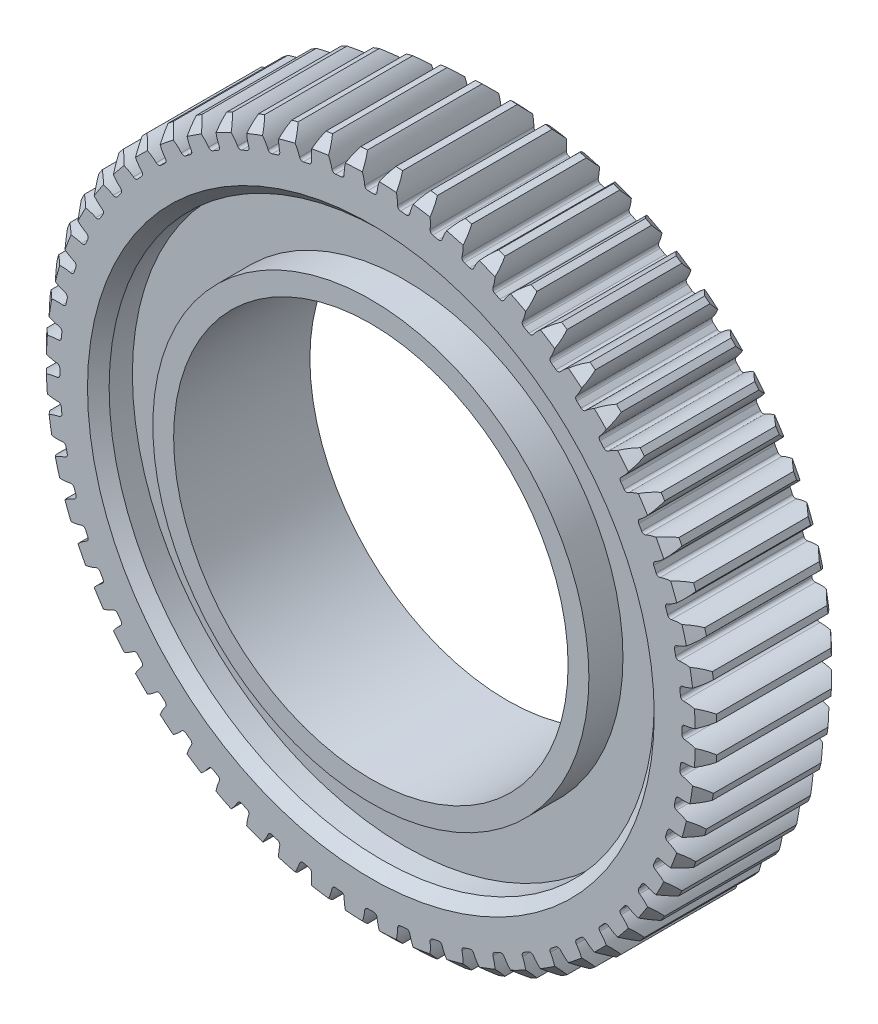
SolidWorks part; units mm, degrees
ref_plane "Front Plane" through (0, 0, 0) normal (0, 0, 1) x (1, 0, 0)
ref_plane "Top Plane" through (0, 0, 0) normal (0, 1, 0) x (1, 0, 0)
ref_plane "Right Plane" through (0, 0, 0) normal (1, 0, 0) x (0, 0, -1)
sketch "Sketch1" plane through (0, 0, 0) normal (0, 0, 1) x (1, 0, 0)
  circle A0 centre (0, 0) radius 47.625 construction
  circle A1 centre (0, 0) radius 49.2125
  dimension "D1" = 95.25
  dimension "D2" = 98.425
extrude "Boss-Extrude1" add sketch "Sketch1" along normal mid plane 20
sketch "Sketch2" plane through (0, 0, 0) normal (0, 0, 1) x (1, 0, 0)
  line L0 (0, 49.2125) -> (0, 0) construction
  line L1 (0, 0) -> (5.1441, 48.9429) construction
  line L2 (0, 0) -> (2.5756, 49.1451) construction
  line L3 (0, 0) -> (-0.8785, 45.6322) construction
  line L4 (-1.2467, 47.6087) -> (1.2467, 47.6087) construction
  line L5 (1.2467, 47.6087) -> (3.7366, 47.4782) construction
  line L6 (-1.8182, 49.1789) -> (0, 44.1835) construction
  circle A0 centre (0, 0) radius 46.0375 construction
  arc A2 (0.8785, 45.6322) -> (-0.8785, 45.6322) centre (0, 0) ccw
  circle A3 centre (0, 0) radius 49.2125 construction
  arc A4 (-0.8785, 45.6322) -> (-2.087, 49.1682) centre (-7.0009, 45.5143) ccw
  arc A5 (0.8785, 45.6322) -> (2.087, 49.1682) centre (7.0009, 45.5143) cw
  circle A6 centre (0, 0) radius 47.625 construction
  circle A7 centre (0, 0) radius 49.2125 construction
  arc A8 (5.1441, 48.9429) -> (-2.087, 49.1682) centre (0, 0) ccw
  dimension "D1" = 6
  dimension "D2" = 3.175
  dimension "D3" = 3.5719
  dimension "D4" = 20
extrude "Cut-Extrude1" cut sketch "Sketch2" against normal through all both and the other way through all contours A5 A8 A4 A2
chamfer "Chamfer1" distance 1.5875 2 edges at (0, -49.2125, 10) (0, -49.2125, -10)
fillet "Fillet1" radius 0.4762 2 edges at (0.8785, 45.6322, 0) (-0.8785, 45.6322, 0)
pattern_circular "CirPattern1" count 60 over 360 about axis through (0, 0, 0) along (0, 0, 1) of "Fillet1", "Cut-Extrude1"
sketch "Sketch3" plane through (0, 0, 10) normal (0, 0, 1) x (1, 0, 0)
  circle A0 centre (0, 0) radius 27
  dimension "D1" = 54
extrude "Cut-Extrude2" cut sketch "Sketch3" against normal blind 54
sketch "Sketch4" plane through (0, 0, 10) normal (0, 0, 1) x (1, 0, 0)
  circle A0 centre (0, 0) radius 27
  circle A1 centre (0, 0) radius 32
  circle A2 centre (0, 0) radius 40
  dimension "D1" = 80
  dimension "D2" = 54
  dimension "D3" = 5
extrude "Cut-Extrude3" cut sketch "Sketch4" against normal blind 5 contours A2 A1
mirror "Mirror1" about plane through (0, 0, 0) normal (0, 0, 1) of "Cut-Extrude3"
chamfer "Chamfer2" distance 1.5875 2 edges at (40, 0, -10) (40, 0, 10)
scale "Scale2" scale about centroid uniform scaling yes scale factor 0.259094
sketch "Sketch5" plane through (0, 0, 2.5909) normal (0, 0, 1) x (1, 0, 0)
  circle A0 centre (0, 0) radius 7.5
  dimension "D1" = 15
extrude "Cut-Extrude4" cut sketch "Sketch5" against normal blind 10
equation "\"Module\"= 1.5875mm"
equation "\"Num of Teeth\"= 60"
equation "\"Pressure Angle\"= 20"
equation "\"D1@Sketch1\"=\"Module\"*\"Num of Teeth\""
equation "\"D2@Sketch1\"=(\"Num of Teeth\" + 2 ) * \"Module\""
equation "\"D1@Sketch2\"=360 / \"Num of Teeth\""
equation "\"D2@Sketch2\"= \"Module\"*2"
equation "\"D3@Sketch2\"=\"Module\" *if(\"Module\" = > 1.25,2.25,2.4)"
equation "\"D4@Sketch2\"=\"Pressure Angle\""
equation "\"D1@Fillet1\"=.3 * \"Module\""
equation "\"D1@CirPattern1\"=\"Num of Teeth\""
equation "\"D1@Chamfer1\"=\"Module\""
equation "\"Hub\"=54"
equation "\"D1@Sketch3\"=\"Hub\""
equation "\"D2@Sketch4\"=54"
equation "\"D1@Chamfer2\"=\"Module\""
